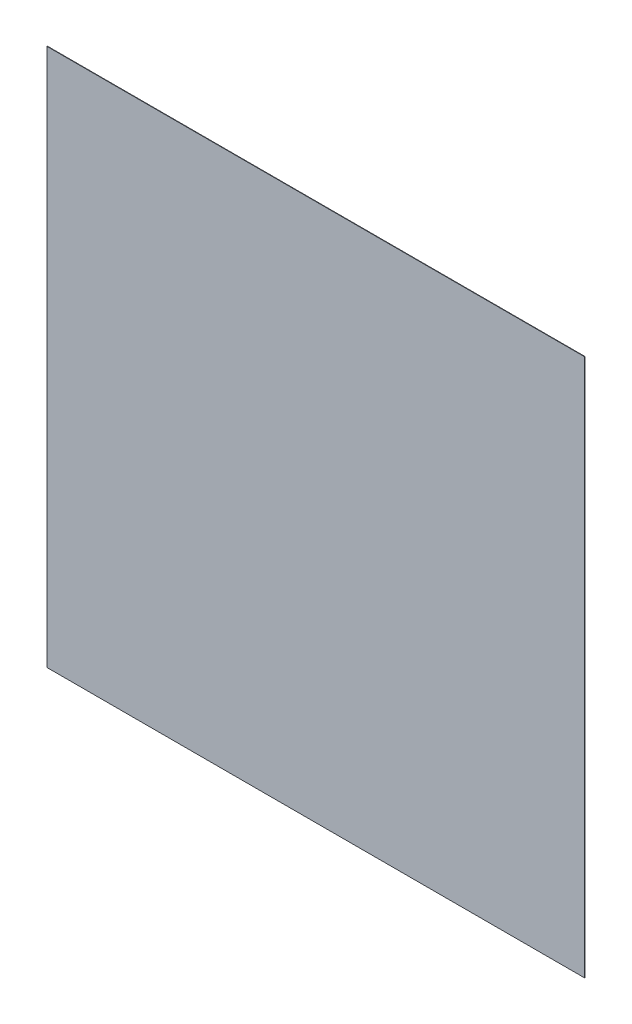
SolidWorks part; units mm, degrees
ref_plane "Front Plane" through (0, 0, 0) normal (0, 0, 1) x (1, 0, 0)
ref_plane "Top Plane" through (0, 0, 0) normal (0, 1, 0) x (1, 0, 0)
ref_plane "Right Plane" through (0, 0, 0) normal (1, 0, 0) x (0, 0, -1)
sketch "Sketch1" plane through (0, 0, 0) normal (0, 0, 1) x (1, 0, 0)
  line L1 (-1524, 1524) -> (1524, 1524)
  line L2 (-1524, 1524) -> (-1524, -1524)
  line L3 (-1524, -1524) -> (1524, -1524)
  line L4 (1524, 1524) -> (1524, -1524)
  line L5 (-1524, 1524) -> (1524, -1524) construction
  line L6 (-1524, -1524) -> (1524, 1524) construction
  point P0 (0, 0)
  dimension "D1" = 3048
extrude "Boss-Extrude1" add sketch "Sketch1" along normal blind 2.54
